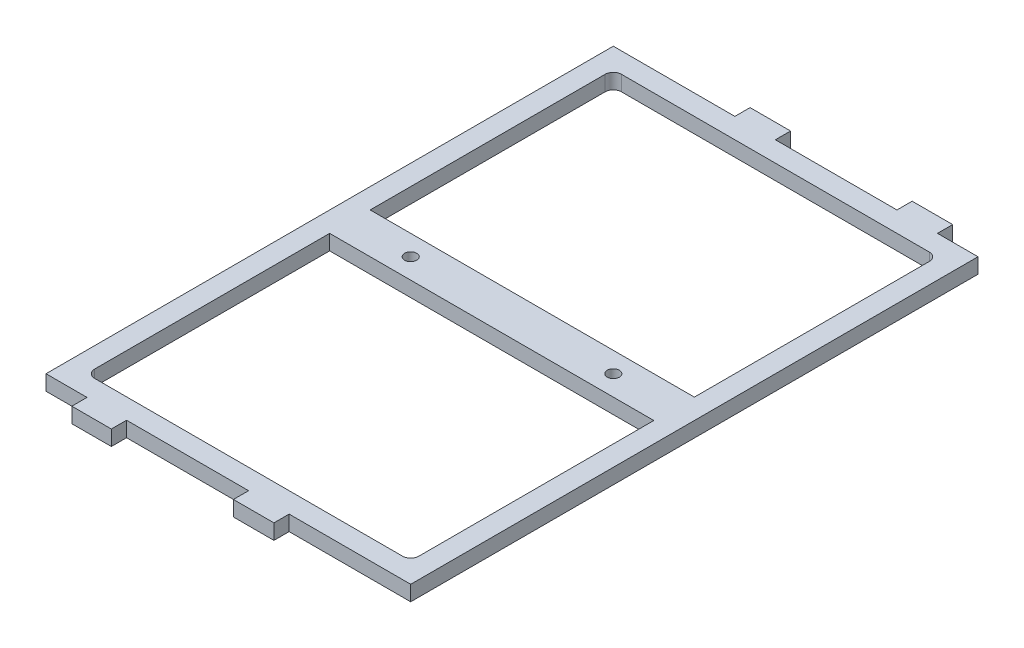
SolidWorks part; units mm, degrees
material "6061-T6 (SS)"
ref_plane "Front Plane" through (0, 0, 0) normal (0, 0, 1) x (1, 0, 0)
ref_plane "Top Plane" through (0, 0, 0) normal (0, 1, 0) x (1, 0, 0)
ref_plane "Right Plane" through (0, 0, 0) normal (1, 0, 0) x (0, 0, -1)
sketch "Sketch1" plane through (0, 0, 0) normal (0, 1, 0) x (1, 0, 0)
  line L0 (50.8, 82.55) -> (-50.8, 82.55)
  line L1 (57.15, 88.9) -> (-57.15, 88.9)
  line L2 (57.15, 88.9) -> (57.15, -88.9)
  line L3 (57.15, -88.9) -> (-57.15, -88.9)
  line L4 (-57.15, 88.9) -> (-57.15, -88.9)
  line L5 (57.15, 88.9) -> (-57.15, -88.9) construction
  line L6 (57.15, -88.9) -> (-57.15, 88.9) construction
  line L7 (-50.8, 82.55) -> (-50.8, -82.55)
  line L8 (50.8, -82.55) -> (-50.8, -82.55)
  line L9 (50.8, 82.55) -> (50.8, -82.55)
  point P0 (0, 0)
  dimension "D1" = 114.3
  dimension "D2" = 177.8
  dimension "D3" = 6.35
extrude "Boss-Extrude1" add sketch "Sketch1" along normal blind 4.7625
sketch "Sketch2" plane through (0, 0, 88.9) normal (0, 0, 1) x (1, 0, 0)
  line L0 (-57.15, 2.3813) -> (57.15, 2.3813) construction
  line L1 (-57.15, 4.7625) -> (-57.15, 0) construction
  line L2 (57.15, 4.7625) -> (57.15, 0) construction
  line L3 (-57.15, 0) -> (57.15, 0) construction
  line L4 (-31.9066, 4.7625) -> (-44.2934, 4.7625)
  line L5 (-31.9066, 4.7625) -> (-31.9066, 0)
  line L6 (-31.9066, 0) -> (-44.2934, 0)
  line L7 (-44.2934, 4.7625) -> (-44.2934, 0)
  line L8 (-31.9066, 4.7625) -> (-44.2934, 0) construction
  line L9 (-31.9066, 0) -> (-44.2934, 4.7625) construction
  line L11 (19.05, 4.7625) -> (6.35, 4.7625)
  line L12 (19.05, 4.7625) -> (19.05, 0)
  line L13 (19.05, 0) -> (6.35, 0)
  line L14 (6.35, 4.7625) -> (6.35, 0)
  line L15 (19.05, 4.7625) -> (6.35, 0) construction
  line L16 (19.05, 0) -> (6.35, 4.7625) construction
  point P6 (-38.1, 2.3813)
  point P13 (12.7, 2.3813)
  dimension "D1" = 19.05
  dimension "D2" = 50.8
  dimension "D3" = 12.7
extrude "Boss-Extrude2" add sketch "Sketch2" along normal blind 4.7625
sketch "Sketch3" plane through (0, 0, -88.9) normal (0, 0, -1) x (-1, 0, 0)
  line L0 (-57.15, 2.3813) -> (57.15, 2.3813) construction
  line L1 (-57.15, 4.7625) -> (-57.15, 0) construction
  line L2 (57.15, 4.7625) -> (57.15, 0) construction
  line L3 (-57.15, 0) -> (57.15, 0) construction
  line L4 (-31.75, 4.7625) -> (-44.45, 4.7625)
  line L5 (-31.75, 4.7625) -> (-31.75, 0)
  line L6 (-31.75, 0) -> (-44.45, 0)
  line L7 (-44.45, 4.7625) -> (-44.45, 0)
  line L8 (-31.75, 4.7625) -> (-44.45, 0) construction
  line L9 (-31.75, 0) -> (-44.45, 4.7625) construction
  line L11 (19.05, 4.7625) -> (6.35, 4.7625)
  line L12 (19.05, 4.7625) -> (19.05, 0)
  line L13 (19.05, 0) -> (6.35, 0)
  line L14 (6.35, 4.7625) -> (6.35, 0)
  line L15 (19.05, 4.7625) -> (6.35, 0) construction
  line L16 (19.05, 0) -> (6.35, 4.7625) construction
  point P6 (-38.1, 2.3812)
  point P13 (12.7, 2.3812)
  dimension "D1" = 12.7
  dimension "D2" = 12.7
  dimension "D3" = 19.05
  dimension "D4" = 50.8
extrude "Boss-Extrude3" add sketch "Sketch3" along normal blind 4.7625
fillet "Fillet1" radius 2.54 4 edges at (50.8, 2.3813, 82.55) (50.8, 2.3813, -82.55) (-50.8, 2.3813, -82.55) (-50.8, 2.3813, 82.55)
sketch "Sketch4" plane through (0, 4.7625, 0) normal (0, 1, 0) x (1, 0, 0)
  line L0 (-57.15, 88.9) -> (-57.15, -88.9) construction
  line L1 (57.15, 6.35) -> (-57.15, 6.35)
  line L2 (57.15, 6.35) -> (57.15, -6.35)
  line L3 (57.15, -6.35) -> (-57.15, -6.35)
  line L4 (-57.15, 6.35) -> (-57.15, -6.35)
  line L5 (57.15, 6.35) -> (-57.15, -6.35) construction
  line L6 (57.15, -6.35) -> (-57.15, 6.35) construction
  point P0 (0, 0)
  dimension "D1" = 12.7
extrude "Boss-Extrude4" add sketch "Sketch4" against normal blind 4.7625
hole_wizard "#6 Clearance Hole1" positions "Sketch6" profile "Sketch5" hole size "#6" standard "Ansi Inch"
sketch "Sketch6" plane through (0, 4.7625, 0) normal (0, 1, 0) x (-1, 0, 0)
  line L0 (-57.15, 0) -> (57.15, 0) construction
  line L1 (-57.15, 88.9) -> (-57.15, -88.9) construction
  line L2 (57.15, -88.9) -> (57.15, 88.9) construction
  line L4 (0, 6.35) -> (0, -6.35) construction
  line L5 (50.8, 6.35) -> (-50.8, 6.35) construction
  line L6 (-50.8, -6.35) -> (50.8, -6.35) construction
  point P0 (31.75, 0)
  point P1 (-31.75, 0)
  dimension "D1" = 31.75
  dimension "D2" = 31.75
sketch "Sketch5" plane through (-31.75, 4.7625, 0) normal (1, 0, 0) x (0, 0, 1)
  line L0 (0, 0) -> (0, 26.5408)
  line L1 (0, 26.5408) -> (1.8986, 25.4)
  line L2 (1.8986, 25.4) -> (1.8986, 0)
  line L5 (1.8986, 0) -> (0, 0)
  line L10 (0, 26.5408) -> (-1.8986, 25.4) construction
  line L11 (0, -6.35) -> (0, 107.95) construction
  dimension "Hole Dia." = 3.7973
  dimension "Hole Depth" = 25.4
  dimension "Drill Angle" = 118
